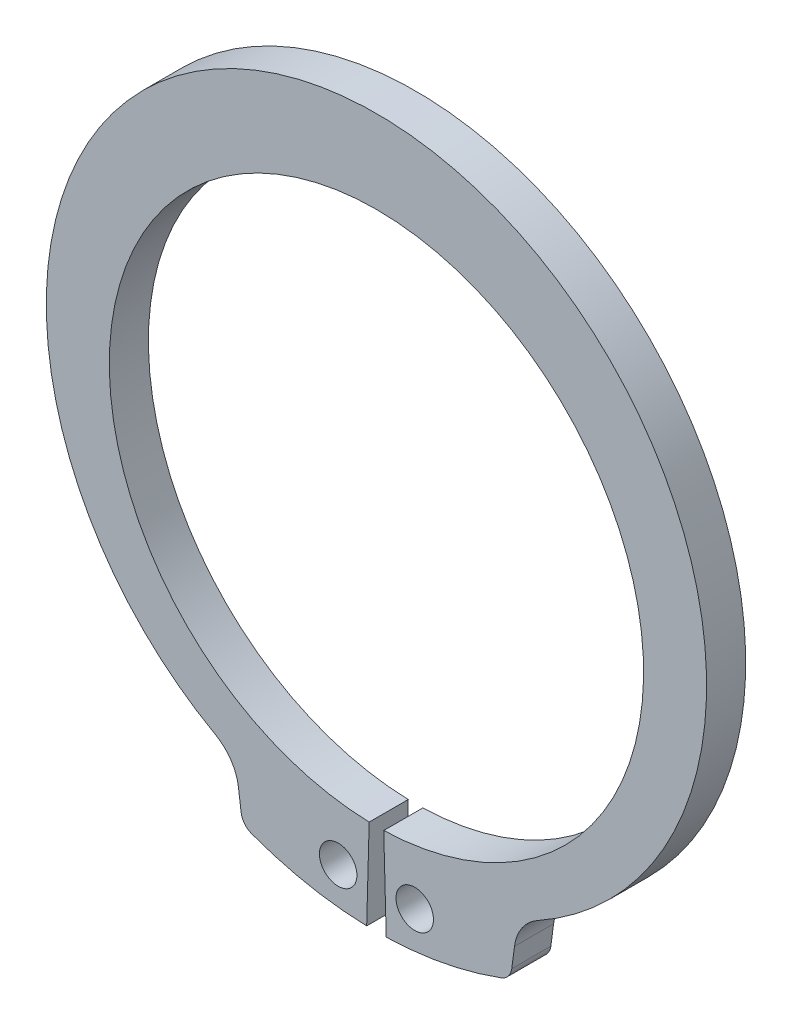
SolidWorks part; units mm, degrees
ref_plane "Plane1" through (0, 0, 0) normal (0, 0, 1) x (1, 0, 0)
ref_plane "Plane2" through (0, 0, 0) normal (0, 1, 0) x (1, 0, 0)
ref_plane "Plane3" through (0, 0, 0) normal (1, 0, 0) x (0, 0, -1)
sketch "Clipboard" plane through (0, 0, 0) normal (0, 0, 1) x (1, 0, 0)
  line L0 (0, 0) -> (5.1, 0)
  line L1 (0, 0) -> (0, 2.8)
  line L2 (0, 0) -> (0, -5.6)
  circle A0 centre (0, 0) radius 1.15
  circle A1 centre (0, 0) radius 17.5
  dimension "HoleDia" = 2.3
  dimension "ShaftDia" = 35
  dimension "LargeSection" = 5.1
  dimension "SmallSection" = 2.8
  dimension "LugSection" = 5.6
sketch "BodySke" plane through (0, 0, 0) normal (0, 0, 1) x (1, 0, 0)
  line L0 (-1.5431, 0) -> (1.5431, 0) construction
  line L1 (0, 0) -> (0, 21.5) construction
  line L2 (0.4473, -16.3939) -> (0.6, -21.9918)
  line L3 (-0.4473, -16.3939) -> (-0.6, -21.9918)
  line L4 (0, 0) -> (11.2489, -18.9067) construction
  line L5 (0, 0) -> (-11.2489, -18.9067) construction
  line L7 (8.4741, -18.5413) -> (8.3063, -19.8154)
  line L8 (-8.4741, -18.5413) -> (-8.3063, -19.8154)
  circle A0 centre (0, 0) radius 16.4 construction
  arc A1 (0.4473, -16.3939) -> (-0.4473, -16.3939) centre (0, 0) ccw
  arc A2 (9.8173, -16.5003) -> (-9.8173, -16.5003) centre (0, 1.2317) ccw construction
  arc A3 (0.6, -21.9918) -> (7.6632, -20.6222) centre (0, 0) ccw
  arc A4 (9.8841, -16.4632) -> (8.4741, -18.5413) centre (11.2489, -18.9067) ccw
  arc A5 (-8.4741, -18.5413) -> (-9.8841, -16.4632) centre (-11.2489, -18.9067) ccw
  arc A6 (-7.6632, -20.6222) -> (-0.6, -21.9918) centre (0, 0) ccw
  arc A7 (9.8841, -16.4632) -> (-9.8841, -16.4632) centre (0, 1.2317) ccw
  arc A8 (-8.5727, -17.7925) -> (8.5727, -17.7925) centre (0, 0) ccw construction
  circle A9 centre (2.35, -19.6097) radius 1.15
  circle A10 centre (-2.35, -19.6097) radius 1.15
  arc A11 (8.3063, -19.8154) -> (7.6632, -20.6222) centre (7.3149, -19.6848) cw
  arc A12 (-8.3063, -19.8154) -> (-7.6632, -20.6222) centre (-7.3149, -19.6848) ccw
  point P28 (8.229, -20.403)
  point P31 (-8.229, -20.403)
  dimension "GrooveDia" = 32.8
  dimension "LugRad" = 22
  dimension "HoleOffsetRad" = 19.75
  dimension "HoleDia" = 2.3
  dimension "D3" = 1
  dimension "LargeRad" = 21.5
  dimension "SmallRad" = 19.2
  dimension "SmallAngle" = 61.503
  dimension "D2" = 15
  dimension "HoleSpacing" = 4.7
  dimension "Gap" = 1.2
extrude "Body" add sketch "BodySke" against normal blind 2.4
sketch "NotSke" plane through (0, 0, 0) normal (0, 0, 1) x (1, 0, 0)
  line L0 (2.35, -18.4597) -> (2.35, -20.7597)
  line L1 (2.35, -20.7597) -> (-2.35, -20.7597)
  line L2 (-2.35, -20.7597) -> (-2.35, -18.4597)
  line L3 (-2.35, -18.4597) -> (2.35, -18.4597)
  circle A0 centre (2.35, -19.6097) radius 1.15 construction
  circle A1 centre (-2.35, -19.6097) radius 1.15 construction
extrude "Notch" [suppressed] cut sketch "NotSke" against normal through all
equation "' \"ShaftDia@Clipboard\" = 10"
equation "' \"Thickness@Body\" = 0.9"
equation "' \"GrooveDia@BodySke\" = 9.4"
equation "' \"LugSection@Clipboard\" = 2.6"
equation "' \"LargeSection@Clipboard\" = 1.7"
equation "' \"SmallSection@Clipboard\" = 1.0"
equation "' \"HoleDia@Clipboard\" = 1.0"
equation "' \"ShaftDia@Clipboard\" = 30"
equation "' \"Thickness@Body\" = 2.4"
equation "' \"GrooveDia@BodySke\" = 28.2"
equation "' \"LugSection@Clipboard\" = 5.6"
equation "' \"LargeSection@Clipboard\" = 4.5"
equation "' \"SmallSection@Clipboard\" = 2.5"
equation "' \"HoleDia@Clipboard\" = 2.3"
equation "\"Gap@BodySke\" =  \"Thickness@Body\" / 2"
equation "\"LargeRad@BodySke\" =  \"GrooveDia@BodySke\" / 2 +  \"LargeSection@Clipboard\""
equation "\"SmallRad@BodySke\" =  \"GrooveDia@BodySke\" / 2 +  \"SmallSection@Clipboard\""
equation "\"LugRad@BodySke\" = \"GrooveDia@BodySke\" / 2 + \"LugSection@Clipboard\""
equation "\"HoleOffsetRad@BodySke\" = (  \"ShaftDia@Clipboard\" / 2 + \"LugRad@BodySke\" ) / 2"
equation "\"HoleSpacing@BodySke\" = \"Gap@BodySke\"  * 2 +  \"HoleDia@Clipboard\""
equation "\"HoleDia@BodySke\" =  \"HoleDia@Clipboard\""
equation "\"SmallAngle@BodySke\" = atn(\"HoleSpacing@BodySke\" / 2 / sqr(\"HoleOffsetRad@BodySke\"  * \"HoleOffsetRad@BodySke\" - (\"HoleSpacing@BodySke\" / 2) * (\"HoleSpacing@BodySke\" / 2) ))  * 9 * ( 180 / 3.141593)"
